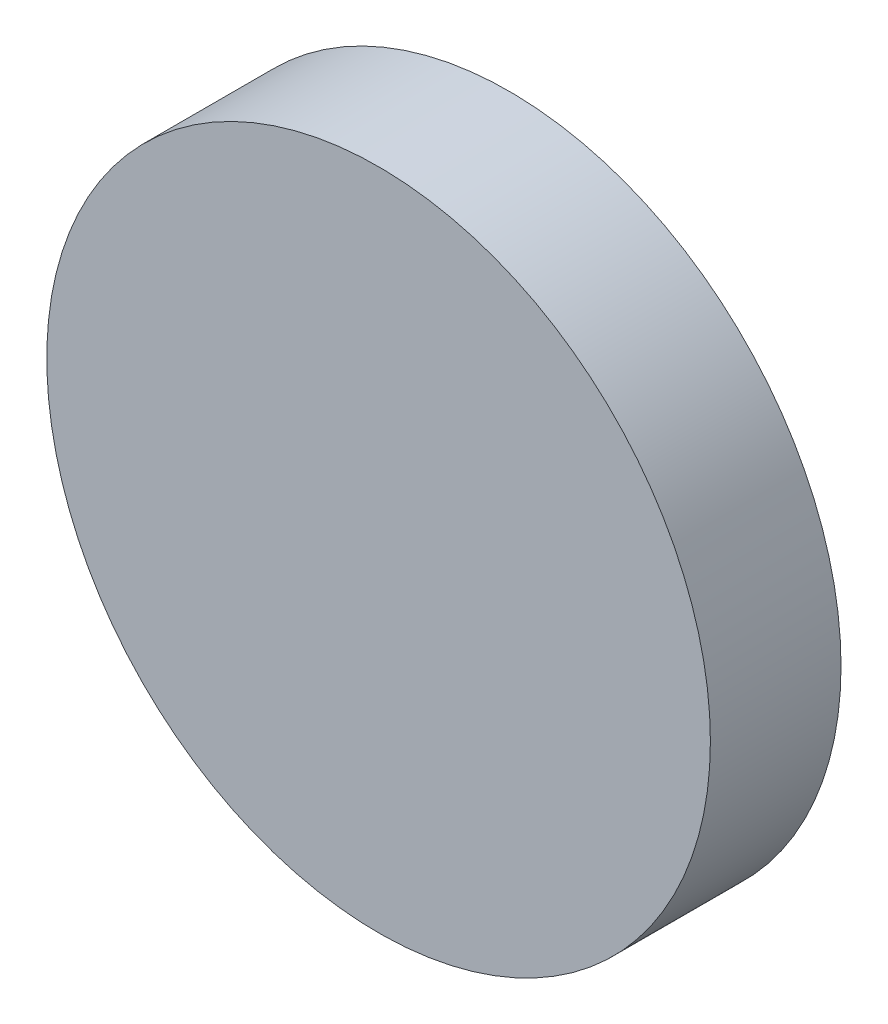
SolidWorks part; units mm, degrees
ref_plane "前视基准面" through (0, 0, 0) normal (0, 0, 1) x (1, 0, 0)
ref_plane "上视基准面" through (0, 0, 0) normal (0, 1, 0) x (1, 0, 0)
ref_plane "右视基准面" through (0, 0, 0) normal (1, 0, 0) x (0, 0, -1)
sketch "草图1" plane through (0, 0, 0) normal (0, 0, 1) x (1, 0, 0)
  circle A0 centre (0, 0) radius 12.7
  dimension "D1" = 25.4
extrude "凸台-拉伸1" add sketch "草图1" along normal blind 5 contours A0
